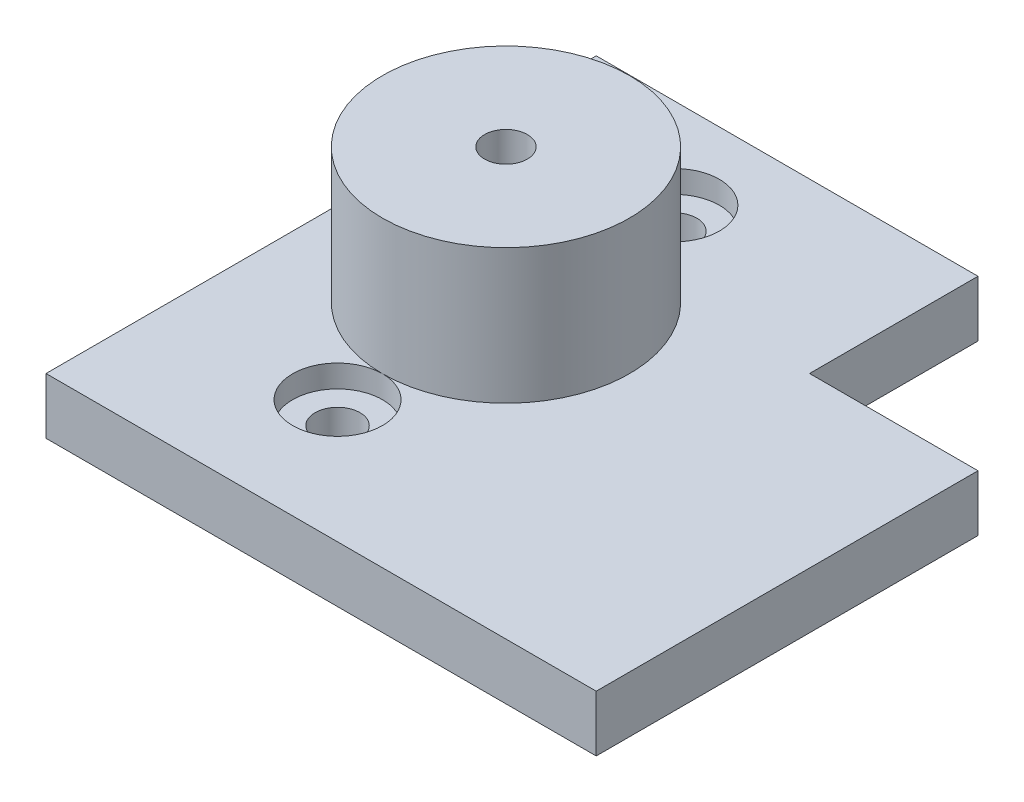
SolidWorks part; units mm, degrees
ref_plane "Front Plane" through (0, 0, 0) normal (0, 0, 1) x (1, 0, 0)
ref_plane "Top Plane" through (0, 0, 0) normal (0, 1, 0) x (1, 0, 0)
ref_plane "Right Plane" through (0, 0, 0) normal (1, 0, 0) x (0, 0, -1)
sketch "Sketch1" plane through (0, 0, 0) normal (0, 1, 0) x (1, 0, 0)
  line L1 (0, 0) -> (49, 0)
  line L2 (0, 0) -> (0, 49)
  line L3 (0, 49) -> (49, 49)
  line L4 (49, 0) -> (49, 49)
  line L5 (49, 49) -> (34, 49)
  line L6 (49, 49) -> (49, 34)
  line L7 (49, 34) -> (34, 34)
  line L8 (34, 49) -> (34, 34)
  circle A0 centre (15, 10.9635) radius 2
  circle A1 centre (15, 25.9635) radius 2
  circle A2 centre (15, 40.9635) radius 2
  dimension "D6" = 4
  dimension "D8" = 4
  dimension "D9" = 4
  dimension "D1" = 49
  dimension "D2" = 49
  dimension "D3" = 15
  dimension "D4" = 15
  dimension "D5" = 15
  dimension "D7" = 15
  dimension "D10" = 15
extrude "Boss-Extrude1" add sketch "Sketch1" along normal blind 5 contours L8 L3 L2 L1 L4 L7 A2 A1 A0
sketch "Sketch2" plane through (0, 5, 0) normal (0, 1, 0) x (1, 0, 0)
  circle A0 centre (15, 40.9635) radius 4
  circle A1 centre (15, 10.9635) radius 4
  dimension "D1" = 8
  dimension "D2" = 8
extrude "Cut-Extrude1" cut sketch "Sketch2" against normal blind 2
sketch "Sketch3" plane through (0, 5, 0) normal (0, 1, 0) x (1, 0, 0)
  circle A0 centre (15, 25.9635) radius 1.9016
  circle A1 centre (15, 25.9635) radius 11
extrude "Boss-Extrude2" add sketch "Sketch3" along normal blind 12
